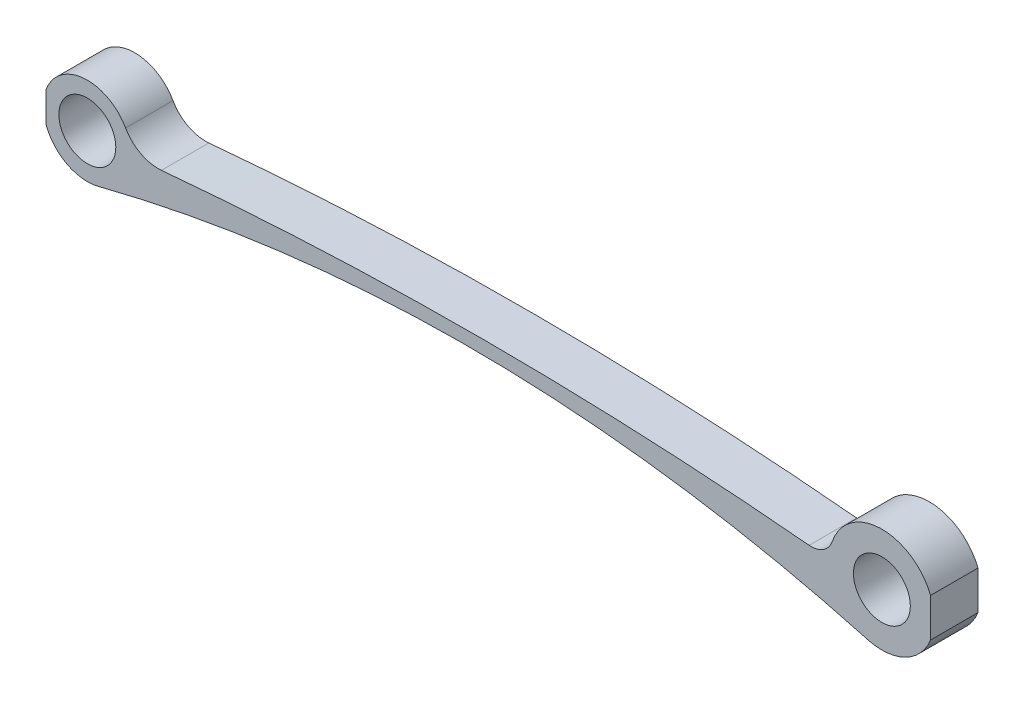
SolidWorks part; units mm, degrees
material "ABS"
ref_plane "Płaszczyzna przednia" through (0, 0, 0) normal (0, 0, 1) x (1, 0, 0)
ref_plane "Płaszczyzna górna" through (0, 0, 0) normal (0, 1, 0) x (1, 0, 0)
ref_plane "Płaszczyzna prawa" through (0, 0, 0) normal (1, 0, 0) x (0, 0, -1)
sketch "Szkic1" plane through (0, 0, 0) normal (0, 0, 1) x (1, 0, 0)
  line L0 (-3, 0) -> (83.7624, 0) construction
  line L1 (40.3812, 0) -> (40.3812, 21.7565) construction
  circle A0 centre (0, 0) radius 3
  circle A1 centre (83.7624, 0) radius 3
  arc A2 (82.2884, -5.3223) -> (78.5373, 1.7882) centre (83.7624, 0) ccw
  arc A3 (4.0339, 2.2831) -> (1.1454, -4.4914) centre (0, 0) ccw
  arc A4 (82.2884, -5.3223) -> (1.1454, -4.4914) centre (40.1549, -157.4605) ccw
  arc A5 (76.0921, 0.2083) -> (78.5373, 1.7882) centre (76.3124, 2.5496) ccw
  arc A6 (76.0921, 0.2083) -> (7.8136, 0.3038) centre (41.4375, -368.2075) ccw
  arc A7 (4.0339, 2.2831) -> (7.8136, 0.3038) centre (7.4563, 4.2201) ccw
  point P6 (80.6194, -3.857)
  point P7 (1.1454, -4.4914)
  point P10 (4.6352, 0)
  point P12 (78.2398, 0)
  dimension "D1" = 83.7624
  dimension "D2" = 6
  dimension "D3" = 5.5226
  dimension "D4" = 4.6352
  dimension "D5" = 6
  dimension "D6" = 2.3516
  dimension "D8" = 3.9325
extrude "Dodanie-wyciągnięcie1" add sketch "Szkic1" along normal blind 5
sketch "Szkic2" plane through (0, 0, 0) normal (0, 0, 1) x (1, 0, 0)
  line L0 (196.2931, 0) -> (-6.6873, 0) construction
  line L1 (88.8955, 4.1341) -> (88.8955, -3.3715)
  line L2 (-4.3568, -2.5646) -> (-4.3568, 2.4871)
  line L4 (-4.3568, 2.4871) -> (-5.0086, 2.4871)
  line L5 (-4.3568, 2.4871) -> (-4.3568, -2.5646)
  line L6 (-4.3568, -2.5646) -> (-5.0086, -2.5646)
  line L7 (-5.0086, 2.4871) -> (-5.0086, -2.5646)
  line L8 (88.8955, -3.3715) -> (194.4479, -3.3715)
  line L9 (88.8955, -3.3715) -> (88.8955, 4.1341)
  line L10 (88.8955, 4.1341) -> (194.4479, 4.1341)
  line L11 (194.4479, -3.3715) -> (194.4479, 4.1341)
extrude "Wytnij-wyciągnięcie3" cut sketch "Szkic2" along normal through all contours L0 L11 L10 L1 | L11 L0 L9 L8 | L0 L5 L4 L7 | L2 L0 L7 L6
